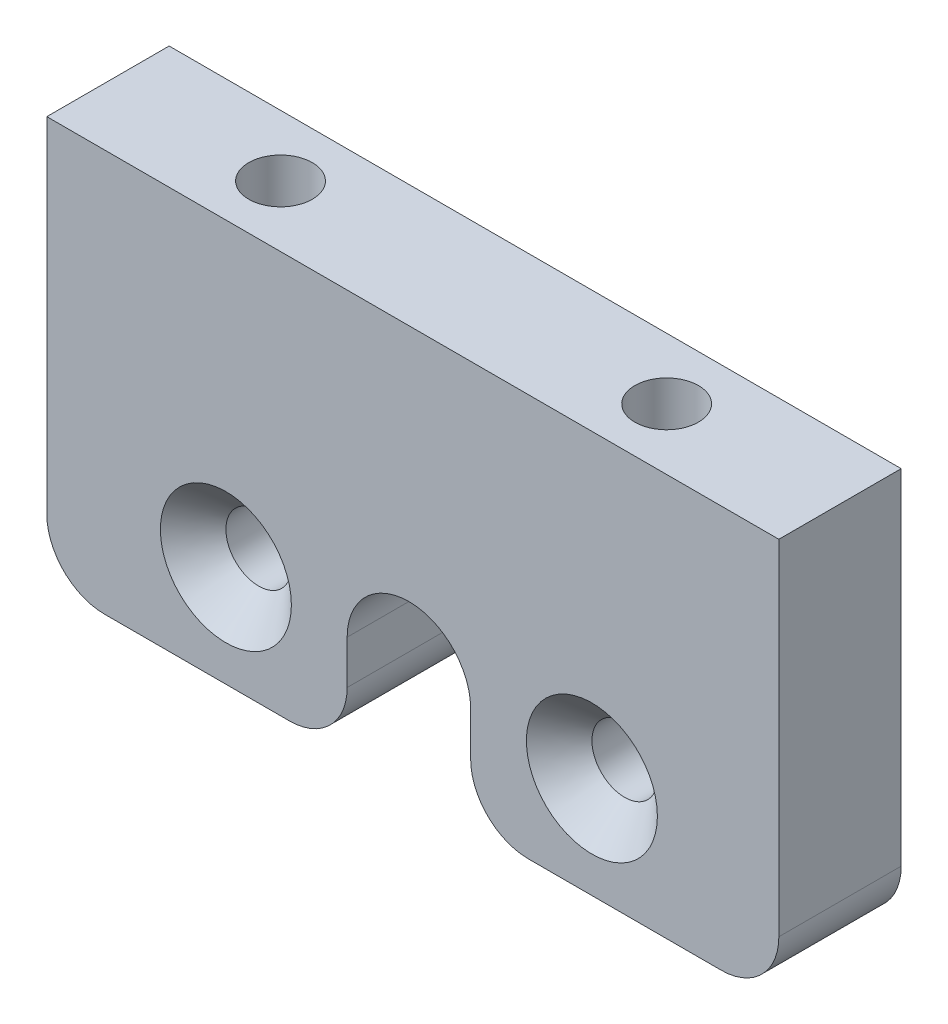
SolidWorks part; units mm, degrees
ref_plane "Front Plane" through (0, 0, 0) normal (0, 0, 1) x (1, 0, 0)
ref_plane "Top Plane" through (0, 0, 0) normal (0, 1, 0) x (1, 0, 0)
ref_plane "Right Plane" through (0, 0, 0) normal (1, 0, 0) x (0, 0, -1)
sketch "Sketch1" plane through (0, 0, -21.6449) normal (0, 0, 1) x (1, 0, 0)
  line L0 (-5.2735, 7.2625) -> (0.3391, 7.2625) construction
  line L1 (3, 7.2625) -> (3, 1.9987)
  line L2 (-3.4097, 7.2625) -> (-3.4097, 1.9987)
  line L3 (3, 1.9987) -> (19, 1.9987)
  line L4 (-3.4097, 1.9987) -> (-19, 1.9987)
  line L5 (19, 1.9987) -> (19, 22.8687)
  line L6 (19, 22.8687) -> (-19, 22.8687)
  line L7 (-19, 22.8687) -> (-19, 1.9987)
  circle A0 centre (-0.2049, 7.2625) radius 9.5 construction
  circle A1 centre (9.2951, 7.2625) radius 1.7
  circle A2 centre (-9.7049, 7.2625) radius 1.7
  arc A4 (3, 7.2625) -> (-3.4097, 7.2625) centre (-0.2049, 7.2625) ccw
extrude "Boss-Extrude1" add sketch "Sketch1" along normal blind 6.35
chamfer "Chamfer1" distance 1.7 angle 45 2 edges at (-8.0049, 7.2625, -15.2949) (10.9951, 7.2625, -15.2949)
sketch "Sketch2" plane through (0, 22.8687, 0) normal (0, 1, 0) x (1, 0, 0)
  line L0 (19, 18.4699) -> (13.1436, 18.4699) construction
  line L1 (19, 15.2949) -> (19, 21.6449) construction
  line L2 (0, 26.9037) -> (0, 22.3463) construction
  line L4 (-10, 26.9037) -> (-10, 22.3463) construction
  line L5 (10, 26.9037) -> (10, 22.3463) construction
  circle A0 centre (10, 18.4699) radius 1.65
  circle A1 centre (-10.0429, 18.4699) radius 1.65
  point P15 (19, 18.4699)
  dimension "D3" = 3.3
  dimension "D4" = 3.3
  dimension "D1" = 10
  dimension "D2" = 10
extrude "Cut-Extrude1" cut sketch "Sketch2" against normal blind 10
fillet "Fillet1" radius 3 4 edges at (-19, 1.9987, -18.4699) (-3.4097, 1.9987, -18.4699) (3, 1.9987, -18.4699) (19, 1.9987, -18.4699)
